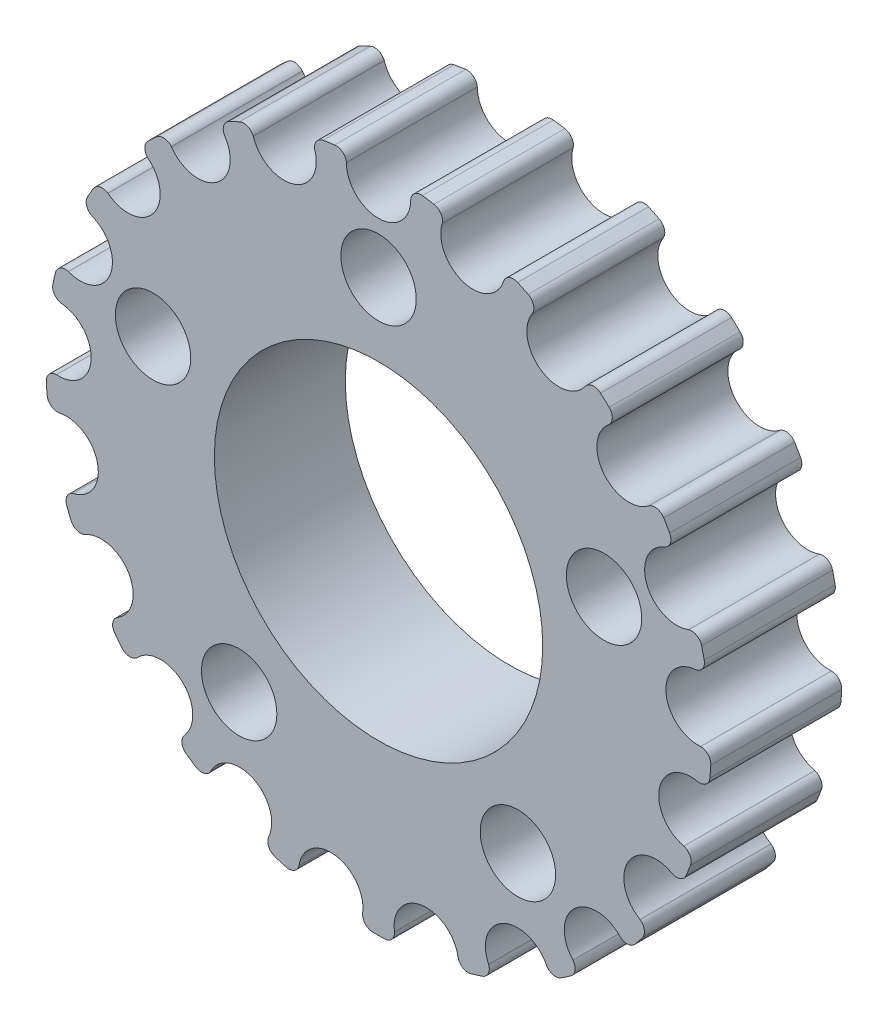
SolidWorks part; units mm, degrees
material "6061-T6 (SS)"
ref_plane "Front Plane" through (0, 0, 0) normal (0, 0, 1) x (1, 0, 0)
ref_plane "Top Plane" through (0, 0, 0) normal (0, 1, 0) x (1, 0, 0)
ref_plane "Right Plane" through (0, 0, 0) normal (1, 0, 0) x (0, 0, -1)
sketch "Pitch diameter" plane through (0, 0, 0) normal (0, 0, 1) x (1, 0, 0)
  circle A0 centre (0, 0) radius 16.7113 construction
  dimension "D1" = 33.4225
sketch "Sketch2" plane through (0, 0, 0) normal (0, 0, 1) x (1, 0, 0)
  circle A0 centre (0, 0) radius 16.1398
  dimension "D1" = 32.2795
extrude "Boss-Extrude1" add sketch "Sketch2" along normal blind 6.35
sketch "Sketch3" plane through (0, 0, 0) normal (0, 0, -1) x (-1, 0, 0)
  line L0 (-1.6121, 16.0591) -> (-1.56, 15.5398)
  line L1 (1.6121, 16.0591) -> (1.56, 15.5398)
  line L2 (-1.56, 15.5398) -> (1.56, 15.5398) construction
  circle A0 centre (0, 0) radius 16.1398 construction
  arc A1 (-1.56, 15.5398) -> (1.56, 15.5398) centre (0, 15.5398) ccw
  circle A2 centre (0, 0) radius 16.1398 construction
  arc A3 (1.6121, 16.0591) -> (-1.6121, 16.0591) centre (0, 0) ccw
  point P10 (0, 15.5398)
  point P15 (0, 13.9798)
  point P16 (0, 16.1398)
  dimension "D1" = 1.56
  dimension "D2" = 2.16
extrude "Cut-Extrude1" cut sketch "Sketch3" against normal through all
fillet "Fillet1" radius 0.5 2 edges at (-1.6121, 16.0591, 3.175) (1.6121, 16.0591, 3.175)
pattern_circular "CirPattern1" count 21 over 360 about axis through (0, 0, 0) along (0, 0, 1) of "Cut-Extrude1", "Fillet1"
sketch "Sketch4" plane through (0, 0, 6.35) normal (0, 0, 1) x (1, 0, 0)
  circle A0 centre (0, 0) radius 7.9629
  dimension "D1" = 15.9258
extrude "Cut-Extrude2" cut sketch "Sketch4" against normal through all
sketch "Sketch5" plane through (0, 0, 6.35) normal (0, 0, 1) x (1, 0, 0)
  line L0 (0, 0) -> (0, 11.5)
  point P0 (0, 0)
  point P7 (0, 0)
  dimension "D1" = 11.5
hole_wizard "#6 Clearance Hole1" positions "Sketch9" profile "Sketch10" hole size "#6" standard "ANSI Inch" end condition through all
sketch "Sketch9" plane through (0, 0, 6.35) normal (0, 0, 1) x (1, 0, 0)
  point P0 (0, 11.5)
sketch "Sketch10" plane through (0, 11.5, 6.35) normal (1, 0, 0) x (0, -1, 0)
  line L0 (0, 0) -> (0, 6.35)
  line L1 (0, 6.35) -> (1.8288, 6.35)
  line L2 (1.8288, 6.35) -> (1.8288, 0)
  line L5 (1.8288, 0) -> (0, 0)
  line L11 (0, -6.35) -> (0, 107.95) construction
  dimension "Thru Hole Dia." = 3.6576
  dimension "Thru Hole Depth" = 6.35
pattern_circular "CirPattern2" count 5 over 360 about axis through (0, 0, 0) along (0, 0, 1) of "#6 Clearance Hole1"
equation "\"NumberOfTeeth\"= 21"
equation "\"Pitch\"= 5mm"
equation "\"PitchDiameter\"= ( \"Pitch\" * \"NumberOfTeeth\" ) / Pi"
equation "\"OD\"= \"PitchDiameter\" - 0.0225in * 2"
equation "\"D1@Pitch diameter\" = \"PitchDiameter\""
equation "\"D1@Sketch2\"=\"OD\""
equation "\"D1@CirPattern1\"=\"NumberOfTeeth\""
